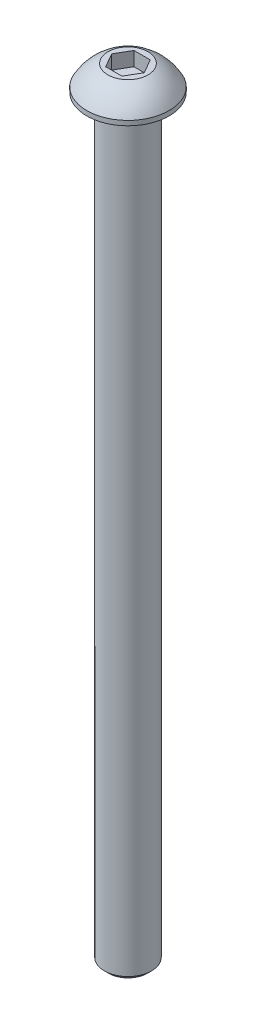
SolidWorks part; units mm, degrees
ref_plane "Front" through (0, 0, 0) normal (0, 0, 1) x (1, 0, 0)
ref_plane "Top" through (0, 0, 0) normal (0, 1, 0) x (1, 0, 0)
ref_plane "Right" through (0, 0, 0) normal (1, 0, 0) x (0, 0, -1)
sketch "Sketch1" plane through (0, 0, 0) normal (0, 0, 1) x (1, 0, 0)
  line L0 (0, 69.088) -> (0, -143.256) construction
  line L1 (0, -127) -> (3.2632, -127)
  line L2 (3.2632, -127) -> (3.9688, -126.2944)
  line L3 (3.9688, -126.2944) -> (3.9688, 0)
  line L4 (3.9688, 0) -> (6.9469, 0)
  line L5 (6.9469, 0) -> (6.9469, 0.7874)
  line L6 (3.3846, 4.2164) -> (0, 4.2164)
  line L7 (0, 4.2164) -> (0, -127)
  line L9 (2.7496, 4.2164) -> (1.3748, 6.5976) construction
  line L10 (1.3748, 6.5976) -> (-1.3748, 6.5976) construction
  line L11 (-1.3748, 6.5976) -> (-2.7496, 4.2164) construction
  line L12 (-2.7496, 4.2164) -> (-1.3748, 1.8351) construction
  line L13 (-1.3748, 1.8351) -> (1.3748, 1.8352) construction
  line L14 (1.3748, 1.8352) -> (2.7496, 4.2164) construction
  arc A0 (6.9469, 0.7874) -> (3.3846, 4.2164) centre (0, -2.8646) ccw
  circle A1 centre (0, 4.2164) radius 2.3813 construction
  dimension "D1" = 45
  dimension "Pitch" = 0.7056
  dimension "Dia" = 7.9375
  dimension "Length" = 127
  dimension "Rib" = 0.7874
  dimension "Height" = 4.2164
  dimension "HeadDia" = 13.8938
  dimension "HexW" = 4.7625
  dimension "D9" = 0.635
revolve "Base-Revolve" add sketch "Sketch1" angle 360 about L0
sketch "Sketch2" plane through (0, 4.2164, 0) normal (0, 1, 0) x (-1, 0, 0)
  line L1 (-2.7496, 0) -> (-1.3748, -2.3812)
  line L2 (-1.3748, -2.3812) -> (1.3748, -2.3812)
  line L3 (1.3748, -2.3812) -> (2.7496, 0)
  line L4 (2.7496, 0) -> (1.3748, 2.3812)
  line L5 (1.3748, 2.3812) -> (-1.3748, 2.3812)
  line L6 (-1.3748, 2.3812) -> (-2.7496, 0)
  circle A0 centre (0, 0) radius 2.3812 construction
extrude "Cut-Extrude1" cut sketch "Sketch2" against normal blind 2.3813
